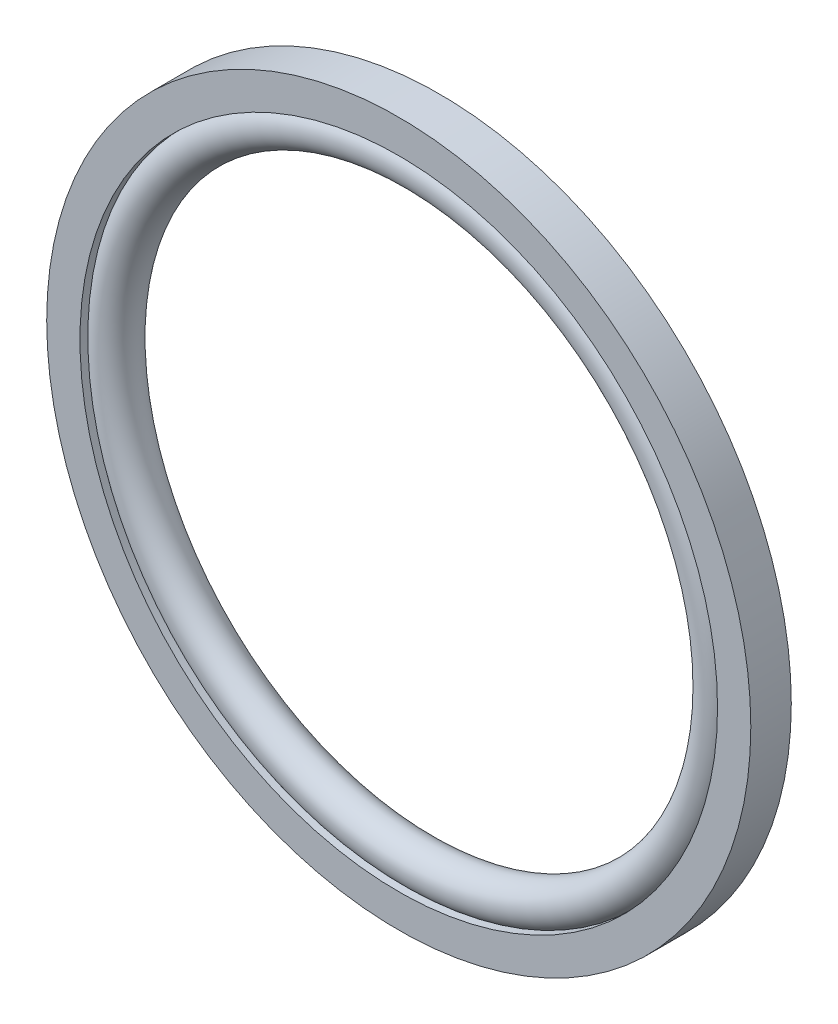
SolidWorks part; units mm, degrees
material "PTFE (general)"
ref_plane "Front Plane" through (0, 0, 0) normal (0, 0, 1) x (1, 0, 0)
ref_plane "Top Plane" through (0, 0, 0) normal (0, 1, 0) x (1, 0, 0)
ref_plane "Right Plane" through (0, 0, 0) normal (1, 0, 0) x (0, 0, -1)
sketch "Sketch1" plane through (0, 0, 0) normal (1, 0, 0) x (0, 0, -1)
  line L0 (-1.4605, 0) -> (1.4605, 0) construction
  line L1 (0, 0) -> (0, 23.2918) construction
  line L2 (-1.4605, 25.4) -> (1.4605, 25.4)
  line L3 (-1.4605, 25.4) -> (-1.4605, 22.9997)
  line L4 (-1.4605, 22.9997) -> (-0.8763, 22.9997)
  line L5 (1.4605, 25.4) -> (1.4605, 22.9997)
  line L6 (0.8763, 22.9997) -> (1.4605, 22.9997)
  line L7 (-1.6383, -25.4) -> (1.6383, -25.4) construction
  line L8 (0, 0) -> (0, -25.4) construction
  arc A0 (-0.8763, 22.9997) -> (0.8763, 22.9997) centre (0, 21.8313) ccw
  point P10 (0, 20.3708)
  dimension "D1" = 1.4605
  dimension "OD" = 50.8
  dimension "ID" = 40.7416
  dimension "Width" = 2.921
  dimension "D2" = 2.6289
  dimension "Groove Width" = 3.2766
  dimension "D3" = 25.4
sketch "Sketch2" plane through (0, 0, 0) normal (1, 0, 0) x (0, 0, -1)
  line L1 (1.4605, 22.9997) -> (-1.4605, 22.9997)
  line L2 (1.4605, 22.9997) -> (1.4605, 25.4)
  line L3 (1.4605, 25.4) -> (-1.4605, 25.4)
  line L4 (-1.4605, 22.9997) -> (-1.4605, 25.4)
revolve "Revolve1" add sketch "Sketch2" angle 360 about L0
sketch "Sketch3" plane through (0, 0, 0) normal (1, 0, 0) x (0, 0, -1)
  line L0 (-0.8763, 22.9997) -> (0.8763, 22.9997)
  arc A0 (-0.8763, 22.9997) -> (0.8763, 22.9997) centre (0, 21.8313) ccw
  arc A1 (-0.8763, 22.9997) -> (0.8763, 22.9997) centre (0, 21.8313) ccw construction
revolve "Revolve2" add sketch "Sketch3" angle 360 about L0
equation "\"D2@Sketch1\"=(\"D1@Sketch1\"*2)*.9"
equation "\"D3@Sketch1\"=\"OD@Sketch1\"/2"
